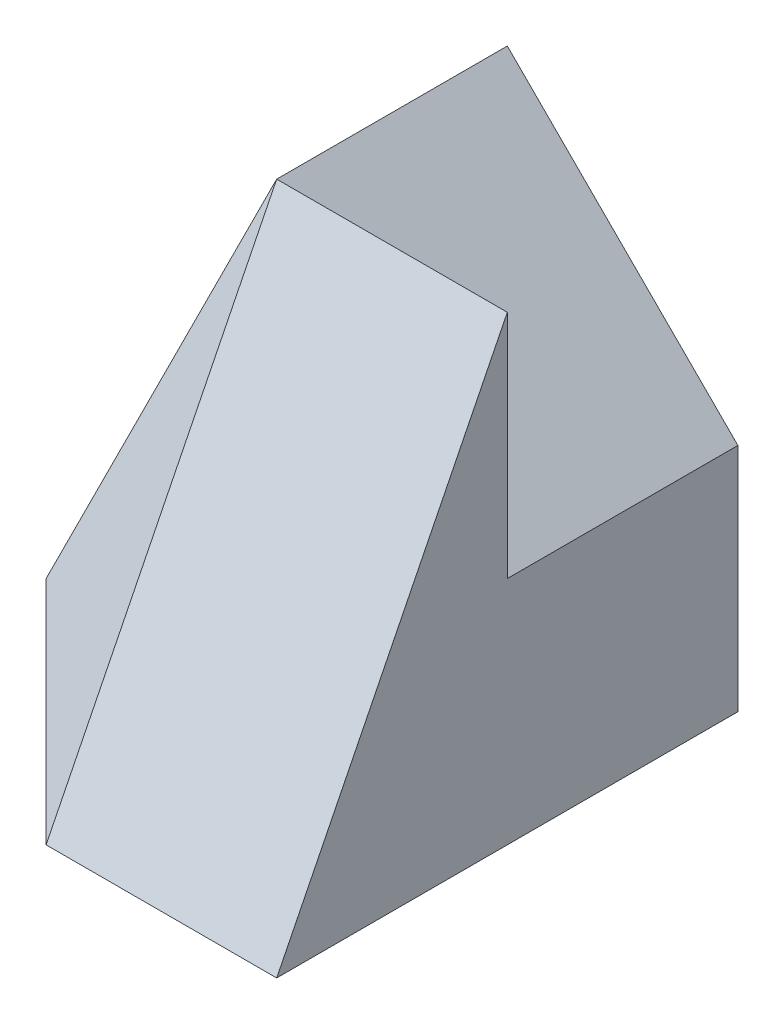
SolidWorks part; units mm, degrees
ref_plane "Front Plane" through (0, 0, 0) normal (0, 0, 1) x (1, 0, 0)
ref_plane "Top Plane" through (0, 0, 0) normal (0, 1, 0) x (1, 0, 0)
ref_plane "Right Plane" through (0, 0, 0) normal (1, 0, 0) x (0, 0, -1)
sketch "Sketch1" plane through (0, 0, 0) normal (0, 0, 1) x (1, 0, 0)
  line L1 (0, 0) -> (20, 0)
  line L2 (0, 0) -> (0, 40)
  line L3 (0, 40) -> (20, 40)
  line L4 (20, 0) -> (20, 40)
  dimension "D1" = 40
  dimension "D2" = 20
extrude "Boss-Extrude1" add sketch "Sketch1" along normal blind 40
sketch "Sketch2" plane through (0, 0, 0) normal (0, 0, -1) x (-1, 0, 0)
  line L0 (0, 0) -> (20, 0)
  line L1 (20, 0) -> (0, 40)
  line L2 (0, 40) -> (0, 0)
  dimension "D1" = 20
extrude "Boss-Extrude2" add sketch "Sketch2" against normal blind 20
sketch "Sketch3" plane through (0, 0, 0) normal (0, 0, -1) x (-1, 0, 0)
  line L0 (0, 40) -> (-20, 20)
  line L1 (-20, 0) -> (-20, 40) construction
  line L2 (-20, 20) -> (-20, 40)
  line L3 (-20, 40) -> (0, 40)
extrude "Cut-Extrude1" cut sketch "Sketch3" against normal blind 20
sketch "Sketch4" plane through (0, 0, 0) normal (-1, 0, 0) x (0, 0, 1)
  line L0 (20, 40) -> (40, 0)
  line L1 (40, 0) -> (40, 40)
  line L2 (40, 40) -> (20, 40)
  line L3 (20, 40) -> (19.966, 40.091)
  line M1 (40, 40) -> (20, 40)
  line M4 (40, 0) -> (40, 40)
extrude "Cut-Extrude2" cut sketch "Sketch4" against normal blind 20 contours L0 M1 M4
ref_plane "Plane1" through (-17.7778, 8.8889, 17.7778) normal (0.6667, -0.3333, -0.6667) x (-0.7454, -0.2981, -0.5963)
sketch "Sketch5" plane through (-17.7778, 8.8889, 17.7778) normal (0.6667, -0.3333, -0.6667) x (-0.7454, -0.2981, -0.5963)
  line L0 (-23.8514, 26.8328) -> (2.9814, -8.9443)
  line L1 (2.9814, -8.9443) -> (-23.8514, -17.8885)
  line L2 (-23.8514, -17.8885) -> (-23.8514, 26.8328)
extrude "Boss-Extrude3" add sketch "Sketch5" along normal blind 20
sketch "Sketch6" plane through (20, 20, 0) normal (0.7071, 0.7071, 0) x (0, 0, -1)
  line L1 (-20, 28.2843) -> (0, 28.2843)
  line L2 (-20, 28.2843) -> (-20, 0)
  line L3 (-20, 0) -> (0, 0)
  line L4 (0, 28.2843) -> (0, 0)
extrude "Cut-Extrude3" cut sketch "Sketch6" along normal blind 20
sketch "Sketch7" plane through (0, 0, 0) normal (0, -1, 0) x (1, 0, 0)
  line L1 (20, 40) -> (-20, 40)
  line L2 (20, 40) -> (20, 0)
  line L3 (20, 0) -> (-20, 0)
  line L4 (-20, 40) -> (-20, 0)
extrude "Cut-Extrude4" cut sketch "Sketch7" along normal blind 20
